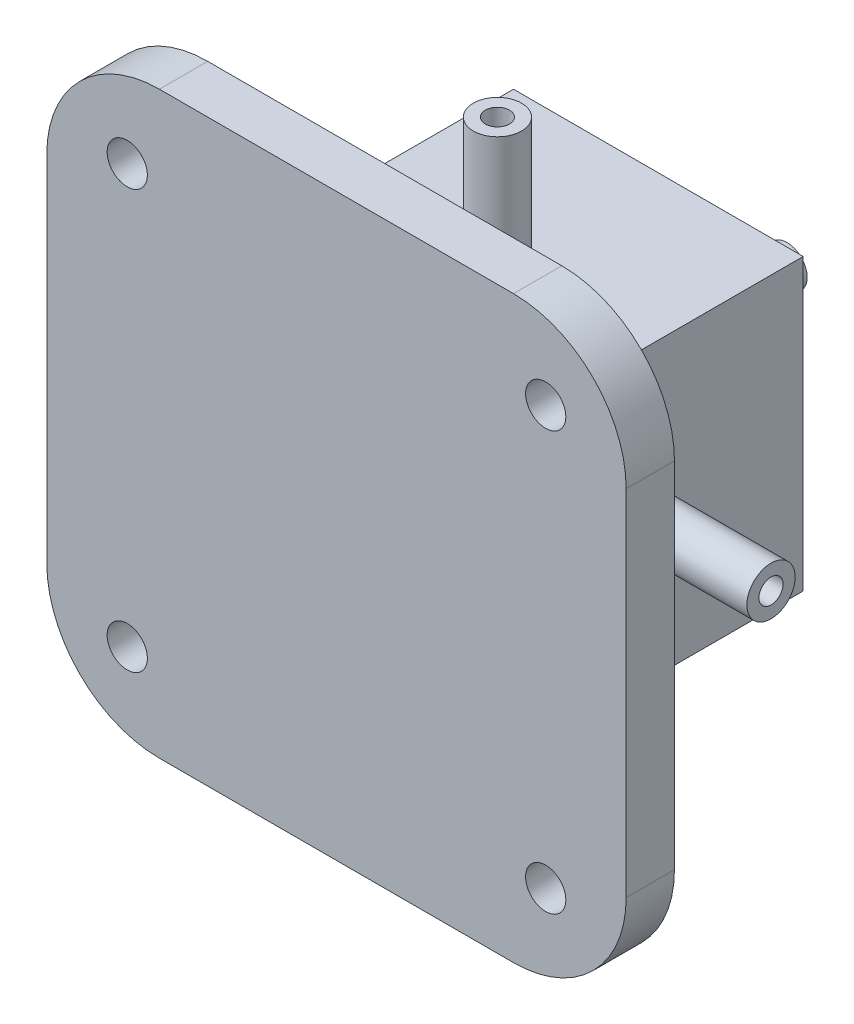
SolidWorks part; units mm, degrees
ref_plane "前视基准面" through (0, 0, 0) normal (0, 0, 1) x (1, 0, 0)
ref_plane "上视基准面" through (0, 0, 0) normal (0, 1, 0) x (1, 0, 0)
ref_plane "右视基准面" through (0, 0, 0) normal (1, 0, 0) x (0, 0, -1)
other "Configuration Table"
sketch "草图1" plane through (0, 0, 0) normal (0, 0, 1) x (1, 0, 0)
  line L1 (-11, -18) -> (11, -18)
  line L2 (-18, -11) -> (-18, 11)
  line L3 (-11, 18) -> (11, 18)
  line L4 (18, -11) -> (18, 11)
  line L5 (-18, -18) -> (18, 18) construction
  line L6 (-18, 18) -> (18, -18) construction
  circle A0 centre (13, 13) radius 1.25
  circle A1 centre (-13, 13) radius 1.25
  circle A2 centre (-13, -13) radius 1.25
  circle A3 centre (13, -13) radius 1.25
  arc A4 (11, -18) -> (18, -11) centre (11, -11) ccw
  arc A5 (-11, -18) -> (-18, -11) centre (-11, -11) cw
  arc A6 (11, 18) -> (18, 11) centre (11, 11) cw
  arc A7 (-18, 11) -> (-11, 18) centre (-11, 11) cw
  point P0 (0, 0)
  point P6 (13, 13)
  dimension "D3" = 5
  dimension "D6" = 2.5
  dimension "D7" = 2.5
  dimension "D4" = 2.5
  dimension "D8" = 2.5
  dimension "D11" = 7
  dimension "D1" = 36
  dimension "D2" = 36
  dimension "D5" = 5
  dimension "D9" = 5
  dimension "D10" = 5
extrude "凸台-拉伸3" add sketch "草图1" along normal blind 3 contours L2 A7 L3 A6 L4 A4 L1 A5 | A1 | A0 | A3 | A2
sketch "草图2" plane through (0, 0, 0) normal (0, 0, 1) x (1, 0, 0)
  line L1 (-9, 9) -> (9, 9)
  line L2 (-9, 9) -> (-9, -9)
  line L3 (-9, -9) -> (9, -9)
  line L4 (9, 9) -> (9, -9)
  line L5 (-9, 9) -> (9, -9) construction
  line L6 (-9, -9) -> (9, 9) construction
  point P0 (0, 0)
  dimension "D1" = 18
  dimension "D2" = 18
extrude "凸台-拉伸4" add sketch "草图2" against normal blind 17
sketch "草图3" plane through (0, 0, -17) normal (0, 0, -1) x (-1, 0, 0)
  circle A0 centre (0, 0) radius 0.85
  dimension "D1" = 1.7
extrude "切除-拉伸2" cut sketch "草图3" against normal blind 12
sketch "草图4" plane through (-9, 0, 0) normal (-1, 0, 0) x (0, 0, 1)
  line L0 (0, 0) -> (-7, 0)
  line L1 (0, 9) -> (0, -9) construction
  circle A0 centre (-7, 0) radius 0.75
extrude "切除-拉伸4" cut sketch "草图4" against normal blind 18 contours A0
sketch "草图5" plane through (0, 9, 0) normal (0, 1, 0) x (1, 0, 0)
  line L0 (0, 0) -> (0, 7)
  line L1 (9, 0) -> (-9, 0) construction
  circle A0 centre (0, 7) radius 0.75
extrude "切除-拉伸5" cut sketch "草图5" against normal blind 18 contours A0
sketch "草图6" plane through (-9, 0, 0) normal (-1, 0, 0) x (0, 0, 1)
  circle A0 centre (-7, 0) radius 1.5
  circle A3 centre (-7, 0) radius 0.75
  dimension "D1" = 1.5
  dimension "D2" = 3
extrude "凸台-拉伸7" add sketch "草图6" along normal blind 8
sketch "草图10" plane through (0, 0, -17) normal (0, 0, -1) x (-1, 0, 0)
  circle A0 centre (0, 0) radius 0.85
  circle A1 centre (0, 0) radius 1.25
  point P0 (0, 0)
  dimension "D1" = 1.7
  dimension "D2" = 2.5
extrude "凸台-拉伸13" add sketch "草图10" along normal blind 8
sketch "草图11" plane through (0, 0, 0) normal (0, 1, 0) x (1, 0, 0)
  line L0 (0, 0) -> (0, 37.5452) construction
pattern_circular "阵列(圆周)1" count 4 over 360 about axis through (0, 0, 0) along (0, 0, 1) of "凸台-拉伸7"
